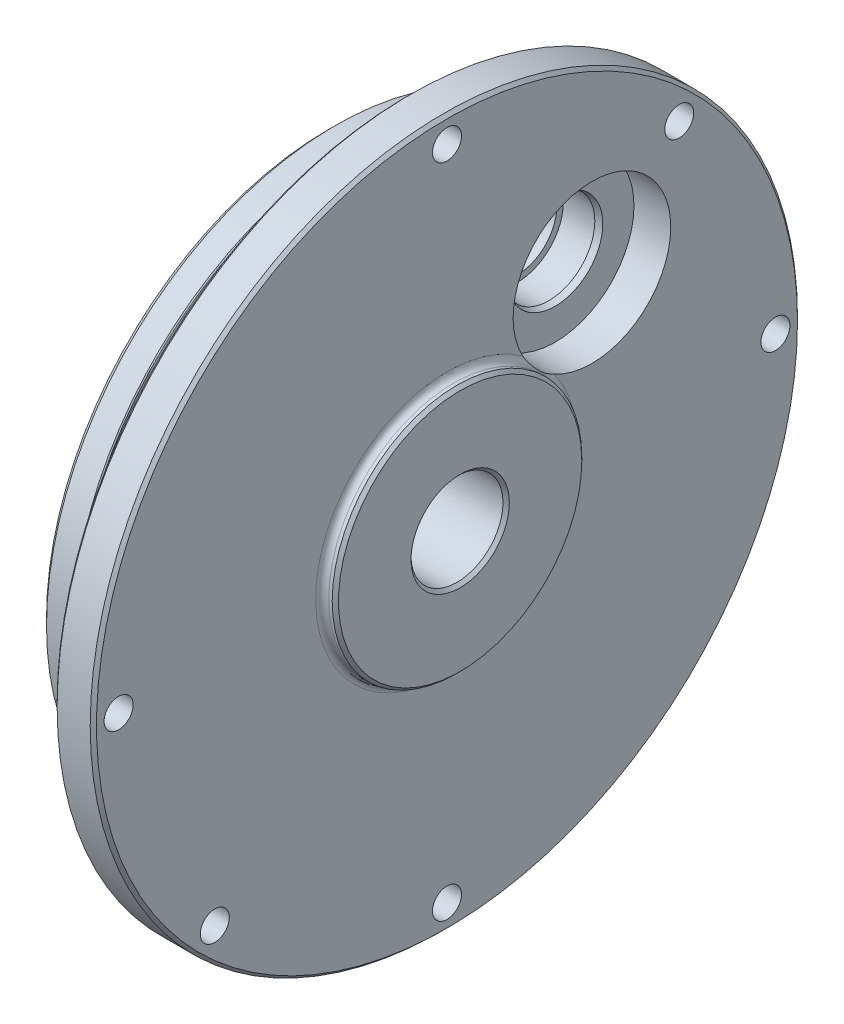
SolidWorks part; units mm, degrees
ref_plane "Front Plane" through (0, 0, 0) normal (0, 0, 1) x (1, 0, 0)
ref_plane "Top Plane" through (0, 0, 0) normal (0, 1, 0) x (1, 0, 0)
ref_plane "Right Plane" through (0, 0, 0) normal (1, 0, 0) x (0, 0, -1)
ref_plane "Plane1" through (0, 0, 0) normal (0, 0, -1) x (-1, 0, 0)
sketch "Sketch1" plane through (0, 0, 0) normal (0, 0, -1) x (-1, 0, 0)
  line L0 (-15.0749, 15.0812) -> (-15.0749, 0)
  line L1 (-15.0749, 0) -> (0, 0)
  line L2 (0, 0) -> (0, 34.8996)
  line L3 (0, 34.8996) -> (-3.937, 34.8996)
  line L4 (-3.937, 34.8996) -> (-3.937, 33.655)
  line L5 (-3.937, 33.655) -> (-6.35, 33.655)
  line L6 (-6.35, 33.655) -> (-6.35, 34.8996)
  line L7 (-6.35, 34.8996) -> (-9.525, 34.8996)
  line L8 (-9.525, 34.8996) -> (-9.525, 42.7355)
  line L9 (-9.525, 42.7355) -> (-14.2875, 42.7355)
  line L10 (-14.2875, 42.7355) -> (-14.2875, 15.8687)
  line L11 (-15.0749, 0) -> (0, 0) construction
  arc A0 (-14.2875, 15.8687) -> (-15.0749, 15.0812) centre (-15.0749, 15.8687) cw
revolve "Revolve1" add sketch "Sketch1" angle 360 about L11
sketch "Sketch2" plane through (15.0749, 0, 0) normal (1, 0, 0) x (0, 0, -1)
  circle A0 centre (0, 0) radius 15.0812
extrude "Boss-Extrude1" add sketch "Sketch2" along normal blind 0.4191
sketch "Sketch3" plane through (15.494, 0, 0) normal (1, 0, 0) x (0, 0, -1)
  circle A0 centre (0, 0) radius 15.0812
extrude "Boss-Extrude2" add sketch "Sketch3" along normal blind 0.381 draft 45
ref_plane "Plane2" through (0, 0, -17.5115) normal (0, 0, 1) x (1, 0, 0)
sketch "Sketch4" plane through (0, 0, -17.5115) normal (0, 0, 1) x (1, 0, 0)
  line L0 (0, 22.274) -> (0, 17.5115)
  line L1 (0, 17.5115) -> (14.6008, 17.5115)
  line L2 (14.6008, 17.5115) -> (14.6008, 27.0365)
  line L3 (14.6008, 27.0365) -> (9.8425, 27.0365)
  line L4 (9.8425, 27.0365) -> (9.8425, 23.0677)
  line L5 (9.8425, 23.0677) -> (5.2705, 23.0677)
  line L6 (5.2705, 23.0677) -> (5.2705, 22.274)
  line L7 (5.2705, 22.274) -> (0, 22.274)
  line L8 (0, 17.5115) -> (14.6008, 17.5115) construction
revolve "Cut-Revolve1" cut sketch "Sketch4" angle 360 about L8
hole_wizard "M3 Clearance Hole1" positions "Sketch6" profile "Sketch5" hole size "M3" standard "ANSI Metric"
sketch "Sketch6" plane through (9.525, 0, 0) normal (-1, 0, 0) x (0, 0, 1)
  point P0 (28.0633, -28.0633)
  point P1 (-28.0633, 28.0633)
  point P2 (39.6875, 0)
  point P3 (-39.6875, 0)
  point P4 (0, -39.6875)
  point P5 (0, 39.6875)
sketch "Sketch5" plane through (9.525, -28.0633, 28.0633) normal (0, 1, 0) x (0, 0, 1)
  line L0 (0, 0) -> (0, 6.35)
  line L1 (0, 6.35) -> (1.7526, 6.35)
  line L2 (1.7526, 6.35) -> (1.7526, 0)
  line L5 (1.7526, 0) -> (0, 0)
  line L11 (0, -6.35) -> (0, 107.95) construction
  dimension "Thru Hole Dia." = 3.5052
  dimension "Thru Hole Depth" = 6.35
hole_wizard "M10 Clearance Hole1" positions "Sketch8" profile "Sketch7" hole size "M10" standard "ANSI Metric"
sketch "Sketch8" plane through (15.875, 0, 0) normal (1, 0, 0) x (0, 0, -1)
  point P0 (0, 0)
sketch "Sketch7" plane through (15.875, 0, 0) normal (0, 1, 0) x (0, 0, -1)
  line L0 (0, 0) -> (0, 15.875)
  line L1 (0, 15.875) -> (5.5562, 15.875)
  line L2 (5.5562, 15.875) -> (5.5562, 0)
  line L5 (5.5562, 0) -> (0, 0)
  line L11 (0, -6.35) -> (0, 107.95) construction
  dimension "Thru Hole Dia." = 11.1125
  dimension "Thru Hole Depth" = 15.875
chamfer "Chamfer1" distance 0.381 angle 45 4 edges at (0, 0, -5.5562) (9.525, 0, 42.7355) (15.875, 0, -5.5562) (14.2875, 0, 42.7355)
chamfer "Chamfer2" distance 0.2042 angle 75 1 edges at (9.8425, 17.5115, -23.0677)
chamfer "Chamfer3" distance 0.7874 angle 45 1 edges at (0, 0, 34.8996)
fillet "Fillet1" radius 0.127 2 edges at (3.937, 0, 34.8996) (6.35, 0, 34.8996)
fillet "Fillet2" radius 0.381 2 edges at (6.35, 0, 33.655) (3.937, 0, 33.655)
